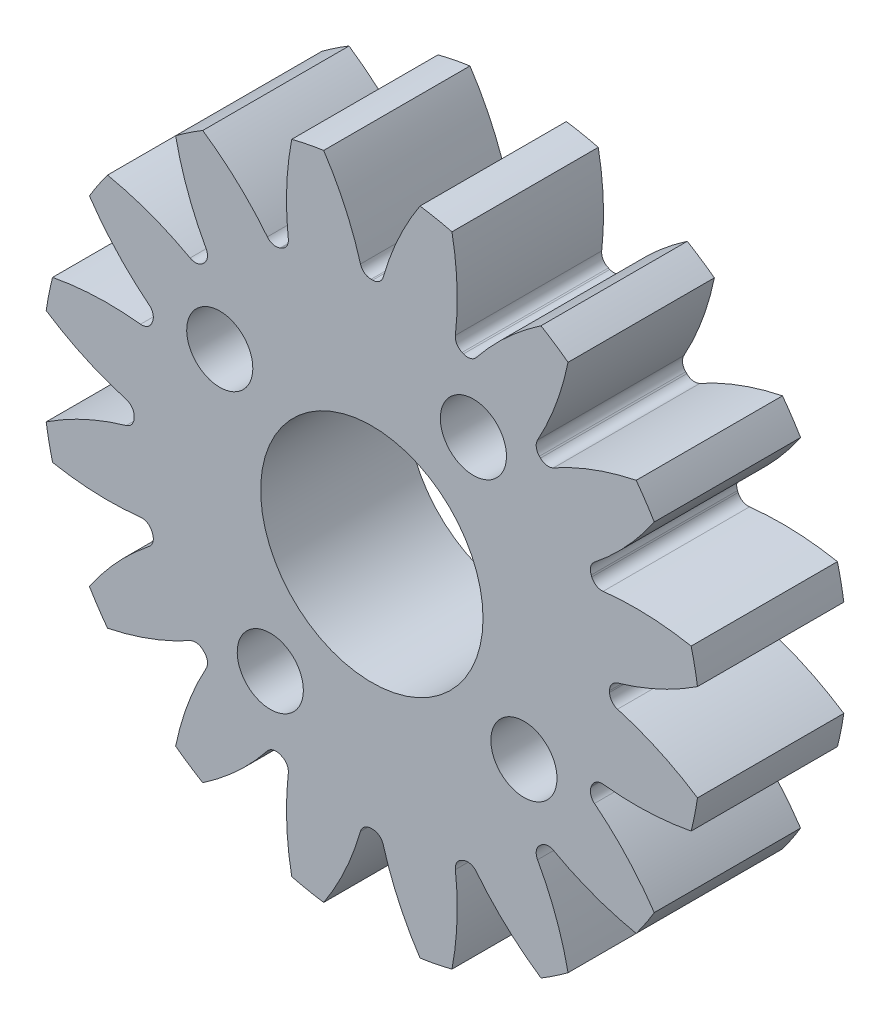
SolidWorks part; units mm, degrees
ref_plane "Front Plane" through (0, 0, 0) normal (0, 0, 1) x (1, 0, 0)
ref_plane "Top Plane" through (0, 0, 0) normal (0, 1, 0) x (1, 0, 0)
ref_plane "Right Plane" through (0, 0, 0) normal (1, 0, 0) x (0, 0, -1)
sketch "Sketch1" plane through (0, 0, 0) normal (0, 0, 1) x (1, 0, 0)
  line L0 (-203.2, 0) -> (203.2, 0) construction
  circle A0 centre (0, 0) radius 14.2875 construction
  circle A1 centre (0, 0) radius 12.7 construction
  circle A2 centre (0, 0) radius 10.3187 construction
  circle A3 centre (0, 0) radius 10.3251 construction
  circle A4 centre (0, 0) radius 6.35 construction
  circle A5 centre (0, 0) radius 10.3187 construction
  dimension "D2" = 1.5875
  dimension "D3" = 3.9688
  dimension "D1" = 3.9688
sketch "Sketch2" plane through (0, 0, 0) normal (1, 0, 0) x (0, 0, -1)
  line L0 (0, 0) -> (-19.05, 0) construction
  line L1 (-19.05, 0) -> (-31.75, 0) construction
  dimension "Overall Width" = 31.75
  dimension "Face Width" = 19.05
sketch "Sketch4" plane through (0, 0, 0) normal (1, 0, 0) x (0, 0, -1)
  line L0 (-31.75, 6.35) -> (-31.75, 10.3251)
  line L1 (-31.75, 10.3251) -> (-19.05, 10.3251)
  line L2 (-19.05, 10.3251) -> (-19.05, 14.2875)
  line L3 (-19.05, 14.2875) -> (0, 14.2875)
  line L4 (0, 14.2875) -> (0, 6.35)
  line L5 (-19.05, 10.3251) -> (-19.05, 0) construction
  line L6 (0, 14.2875) -> (0, -14.2875) construction
  line L7 (-19.05, 10.3251) -> (0, 10.3251) construction
  line L12 (-31.75, 6.35) -> (0, 6.35)
revolve "Revolve1" add sketch "Sketch4" angle 360 about L1
fillet "Fillet2" radius 0.2858 4 edges at (0, 10.3251, 31.75) (0, 10.3251, 19.05) (0, 14.2875, 19.05) (0, 14.2875, 0)
sketch "Sketch7" plane through (0, 0, 19.05) normal (0, 0, 1) x (1, 0, 0)
  line L0 (0, 0) -> (0, 14.2875) construction
  line L1 (1.2448, 12.6388) -> (1.9701, 14.151) construction
  line L3 (2.7874, 14.013) -> (2.4776, 12.456) construction
  line L4 (2.4776, 12.456) -> (2.0131, 10.1205) construction
  line L5 (0, 0) -> (2.0131, 10.1205) construction
  line L6 (1.2448, 12.6388) -> (0, 0) construction
  line L7 (1.2448, 12.6388) -> (1.4004, 14.2187) construction
  line L8 (1.2448, 12.6388) -> (0, 0) construction
  circle A0 centre (0, 0) radius 14.2875 construction
  arc A1 (-0.0331, 10.3187) -> (0.0331, 10.3187) centre (0, 0) cw
  circle A2 centre (0, 0) radius 10.3187 construction
  arc A3 (-1.2448, 12.6388) -> (1.2448, 12.6388) centre (0, 0) cw construction
  circle A4 centre (0, 0) radius 12.7 construction
  arc A5 (3.4772, 13.8579) -> (2.0907, 14.1337) centre (0, 0) ccw construction
  arc A6 (1.2448, 12.6388) -> (3.6866, 12.1531) centre (0, 0) cw construction
  arc A7 (-2.0907, 14.1337) -> (2.0907, 14.1337) centre (0, 0) cw
  arc A8 (0.4923, 10.6631) -> (2.0907, 14.1337) centre (12.6957, 7.1464) cw
  arc A9 (-0.4923, 10.6631) -> (-2.0907, 14.1337) centre (-12.6957, 7.1464) ccw
  arc A10 (-0.0331, 10.3187) -> (-0.4923, 10.6631) centre (-0.0346, 10.795) cw
  arc A11 (0.0331, 10.3187) -> (0.4923, 10.6631) centre (0.0346, 10.795) ccw
  point P26 (-0.3963, 10.3111)
  point P29 (0.3963, 10.3111)
  dimension "D4" = 0.4763
  dimension "D5" = 12.7
  dimension "D3" = 20
  dimension "D1" = 4.9873
  dimension "D2" = 2.4936
extrude "Cut-Extrude2" cut sketch "Sketch7" against normal through all
pattern_circular "CirPattern1" count 16 over 360 about axis through (0, 0, 0) along (0, 0, 1) of "Cut-Extrude2"
sketch "Sketch9" [suppressed] plane through (0, 0, 0) normal (0, 0, 1) x (1, 0, 0)
  circle A0 centre (0, 0) radius 10.3187 construction
  circle A1 centre (0, 0) radius 10.3187
ref_plane "Plane1" through (0, 0, 0) normal (0, 0, -1) x (-1, 0, 0)
ref_plane "Plane2" through (0, 0, 31.75) normal (0, 0, 1) x (1, 0, 0)
sketch "Sketch10" plane through (0, 0, 31.75) normal (0, 0, 1) x (1, 0, 0)
  circle A0 centre (0, 0) radius 29.0934
extrude "Cut-Extrude3" cut sketch "Sketch10" against normal blind 15.24
sketch "Sketch11" plane through (0, 0, 0) normal (0, 0, -1) x (-1, 0, 0)
  circle A0 centre (0, 0) radius 20.5552
extrude "Cut-Extrude4" cut sketch "Sketch11" against normal blind 10.16
sketch "Sketch12" plane through (0, 0, 16.51) normal (0, 0, 1) x (1, 0, 0)
  circle A0 centre (0, 0) radius 7.9171
  circle A1 centre (0, 0) radius 4.826
  dimension "D1" = 9.652
extrude "Boss-Extrude1" add sketch "Sketch12" against normal up to surface (6.35 mm away) up to face at (0, 6.35, 10.16)
sketch "Эскиз1" plane through (0, 0, 0) normal (0, 0, -1) x (-1, 0, 0)
  line L0 (0, 0) -> (17.9765, 12.0041) construction
  circle A0 centre (6.601, 4.408) radius 1.4351
  circle A1 centre (4.408, -6.601) radius 1.4351
  circle A2 centre (-6.601, -4.408) radius 1.4351
  circle A3 centre (-4.408, 6.601) radius 1.4351
  dimension "D3" = 2.8702
  dimension "D2" = 7.9375
  dimension "D1" = 4
extrude "Вырез-Вытянуть1" cut sketch "Эскиз1" against normal through all
sketch "Sketch13" plane through (0, 0, 16.51) normal (0, 0, 1) x (1, 0, 0)
  circle A0 centre (-4.408, -6.601) radius 1.4351 construction
  circle A1 centre (-4.408, -6.601) radius 1.4351
  circle A2 centre (6.601, -4.408) radius 1.4351 construction
  circle A3 centre (4.408, 6.601) radius 1.4351 construction
  circle A4 centre (-6.601, 4.408) radius 1.4351 construction
  circle A5 centre (6.601, -4.408) radius 1.4351
  circle A6 centre (4.408, 6.601) radius 1.4351
  circle A7 centre (-6.601, 4.408) radius 1.4351
  circle A8 centre (0, 0) radius 4.826 construction
  circle A9 centre (0, 0) radius 4.826
  arc A96 (-7.3402, -12.2578) -> (-4.5354, -9.663) centre (-14.4641, -1.7439) ccw
  arc A97 (-3.9794, -9.5206) -> (-4.5354, -9.663) centre (-4.1631, -9.96) ccw
  arc A98 (-3.9794, -9.5206) -> (-3.9182, -9.5459) centre (0, 0) ccw
  arc A99 (-3.6258, -10.0398) -> (-3.9182, -9.5459) centre (-4.099, -9.9865) ccw
  arc A100 (-3.6258, -10.0398) -> (-3.4772, -13.8579) centre (8.9945, -11.4608) ccw
  arc A101 (-3.4772, -13.8579) -> (-2.0907, -14.1337) centre (0, 0) ccw
  arc A102 (-2.0907, -14.1337) -> (-0.4923, -10.6631) centre (-12.6957, -7.1464) ccw
  arc A103 (-0.0331, -10.3187) -> (-0.4923, -10.6631) centre (-0.0346, -10.795) ccw
  arc A104 (-0.0331, -10.3187) -> (0.0331, -10.3187) centre (0, 0) ccw
  arc A105 (0.4923, -10.6631) -> (0.0331, -10.3187) centre (0.0346, -10.795) ccw
  arc A106 (0.4923, -10.6631) -> (2.0907, -14.1337) centre (12.6957, -7.1464) ccw
  arc A107 (2.0907, -14.1337) -> (3.4772, -13.8579) centre (0, 0) ccw
  arc A108 (3.4772, -13.8579) -> (3.6258, -10.0398) centre (-8.9945, -11.4608) ccw
  arc A109 (3.9182, -9.5459) -> (3.6258, -10.0398) centre (4.099, -9.9865) ccw
  arc A110 (3.9182, -9.5459) -> (3.9794, -9.5206) centre (0, 0) ccw
  arc A111 (4.5354, -9.663) -> (3.9794, -9.5206) centre (4.1631, -9.96) ccw
  arc A112 (4.5354, -9.663) -> (7.3402, -12.2578) centre (14.4641, -1.7439) ccw
  arc A113 (7.3402, -12.2578) -> (8.5157, -11.4724) centre (0, 0) ccw
  arc A114 (8.5157, -11.4724) -> (7.1918, -7.8881) centre (-3.924, -14.0305) ccw
  arc A115 (7.273, -7.3198) -> (7.1918, -7.8881) centre (7.6087, -7.6577) ccw
  arc A116 (7.273, -7.3198) -> (7.3198, -7.273) centre (0, 0) ccw
  arc A117 (7.8881, -7.1918) -> (7.3198, -7.273) centre (7.6577, -7.6087) ccw
  arc A118 (7.8881, -7.1918) -> (11.4724, -8.5157) centre (14.0305, 3.924) ccw
  arc A119 (11.4724, -8.5157) -> (12.2578, -7.3402) centre (0, 0) ccw
  arc A120 (12.2578, -7.3402) -> (9.663, -4.5354) centre (1.7439, -14.4641) ccw
  arc A121 (9.5206, -3.9794) -> (9.663, -4.5354) centre (9.96, -4.1631) ccw
  arc A122 (9.5206, -3.9794) -> (9.5459, -3.9182) centre (0, 0) ccw
  arc A123 (10.0398, -3.6258) -> (9.5459, -3.9182) centre (9.9865, -4.099) ccw
  arc A124 (10.0398, -3.6258) -> (13.8579, -3.4772) centre (11.4608, 8.9945) ccw
  arc A125 (13.8579, -3.4772) -> (14.1337, -2.0907) centre (0, 0) ccw
  arc A126 (14.1337, -2.0907) -> (10.6631, -0.4923) centre (7.1464, -12.6957) ccw
  arc A127 (10.3187, -0.0331) -> (10.6631, -0.4923) centre (10.795, -0.0346) ccw
  arc A128 (10.3187, -0.0331) -> (10.3187, 0.0331) centre (0, 0) ccw
  arc A129 (10.6631, 0.4923) -> (10.3187, 0.0331) centre (10.795, 0.0346) ccw
  arc A130 (10.6631, 0.4923) -> (14.1337, 2.0907) centre (7.1464, 12.6957) ccw
  arc A131 (14.1337, 2.0907) -> (13.8579, 3.4772) centre (0, 0) ccw
  arc A132 (13.8579, 3.4772) -> (10.0398, 3.6258) centre (11.4608, -8.9945) ccw
  arc A133 (9.5459, 3.9182) -> (10.0398, 3.6258) centre (9.9865, 4.099) ccw
  arc A134 (9.5459, 3.9182) -> (9.5206, 3.9794) centre (0, 0) ccw
  arc A135 (9.663, 4.5354) -> (9.5206, 3.9794) centre (9.96, 4.1631) ccw
  arc A136 (9.663, 4.5354) -> (12.2578, 7.3402) centre (1.7439, 14.4641) ccw
  arc A137 (12.2578, 7.3402) -> (11.4724, 8.5157) centre (0, 0) ccw
  arc A138 (11.4724, 8.5157) -> (7.8881, 7.1918) centre (14.0305, -3.924) ccw
  arc A139 (7.3198, 7.273) -> (7.8881, 7.1918) centre (7.6577, 7.6087) ccw
  arc A140 (7.3198, 7.273) -> (7.273, 7.3198) centre (0, 0) ccw
  arc A141 (7.1918, 7.8881) -> (7.273, 7.3198) centre (7.6087, 7.6577) ccw
  arc A142 (7.1918, 7.8881) -> (8.5157, 11.4724) centre (-3.924, 14.0305) ccw
  arc A143 (8.5157, 11.4724) -> (7.3402, 12.2578) centre (0, 0) ccw
  arc A144 (7.3402, 12.2578) -> (4.5354, 9.663) centre (14.4641, 1.7439) ccw
  arc A145 (3.9794, 9.5206) -> (4.5354, 9.663) centre (4.1631, 9.96) ccw
  arc A146 (3.9794, 9.5206) -> (3.9182, 9.5459) centre (0, 0) ccw
  arc A147 (3.6258, 10.0398) -> (3.9182, 9.5459) centre (4.099, 9.9865) ccw
  arc A148 (3.6258, 10.0398) -> (3.4772, 13.8579) centre (-8.9945, 11.4608) ccw
  arc A149 (3.4772, 13.8579) -> (2.0907, 14.1337) centre (0, 0) ccw
  arc A150 (2.0907, 14.1337) -> (0.4923, 10.6631) centre (12.6957, 7.1464) ccw
  arc A151 (0.0331, 10.3187) -> (0.4923, 10.6631) centre (0.0346, 10.795) ccw
  arc A152 (0.0331, 10.3187) -> (-0.0331, 10.3187) centre (0, 0) ccw
  arc A153 (-0.4923, 10.6631) -> (-0.0331, 10.3187) centre (-0.0346, 10.795) ccw
  arc A154 (-0.4923, 10.6631) -> (-2.0907, 14.1337) centre (-12.6957, 7.1464) ccw
  arc A155 (-2.0907, 14.1337) -> (-3.4772, 13.8579) centre (0, 0) ccw
  arc A156 (-3.4772, 13.8579) -> (-3.6258, 10.0398) centre (8.9945, 11.4608) ccw
  arc A157 (-3.9182, 9.5459) -> (-3.6258, 10.0398) centre (-4.099, 9.9865) ccw
  arc A158 (-3.9182, 9.5459) -> (-3.9794, 9.5206) centre (0, 0) ccw
  arc A159 (-4.5354, 9.663) -> (-3.9794, 9.5206) centre (-4.1631, 9.96) ccw
  arc A160 (-4.5354, 9.663) -> (-7.3402, 12.2578) centre (-14.4641, 1.7439) ccw
  arc A161 (-7.3402, 12.2578) -> (-8.5157, 11.4724) centre (0, 0) ccw
  arc A162 (-8.5157, 11.4724) -> (-7.1918, 7.8881) centre (3.924, 14.0305) ccw
  arc A163 (-7.273, 7.3198) -> (-7.1918, 7.8881) centre (-7.6087, 7.6577) ccw
  arc A164 (-7.273, 7.3198) -> (-7.3198, 7.273) centre (0, 0) ccw
  arc A165 (-7.8881, 7.1918) -> (-7.3198, 7.273) centre (-7.6577, 7.6087) ccw
  arc A166 (-7.8881, 7.1918) -> (-11.4724, 8.5157) centre (-14.0305, -3.924) ccw
  arc A167 (-11.4724, 8.5157) -> (-12.2578, 7.3402) centre (0, 0) ccw
  arc A168 (-12.2578, 7.3402) -> (-9.663, 4.5354) centre (-1.7439, 14.4641) ccw
  arc A169 (-9.5206, 3.9794) -> (-9.663, 4.5354) centre (-9.96, 4.1631) ccw
  arc A170 (-9.5206, 3.9794) -> (-9.5459, 3.9182) centre (0, 0) ccw
  arc A171 (-10.0398, 3.6258) -> (-9.5459, 3.9182) centre (-9.9865, 4.099) ccw
  arc A172 (-10.0398, 3.6258) -> (-13.8579, 3.4772) centre (-11.4608, -8.9945) ccw
  arc A173 (-13.8579, 3.4772) -> (-14.1337, 2.0907) centre (0, 0) ccw
  arc A174 (-14.1337, 2.0907) -> (-10.6631, 0.4923) centre (-7.1464, 12.6957) ccw
  arc A175 (-10.3187, 0.0331) -> (-10.6631, 0.4923) centre (-10.795, 0.0346) ccw
  arc A176 (-10.3187, 0.0331) -> (-10.3187, -0.0331) centre (0, 0) ccw
  arc A177 (-10.6631, -0.4923) -> (-10.3187, -0.0331) centre (-10.795, -0.0346) ccw
  arc A178 (-10.6631, -0.4923) -> (-14.1337, -2.0907) centre (-7.1464, -12.6957) ccw
  arc A179 (-14.1337, -2.0907) -> (-13.8579, -3.4772) centre (0, 0) ccw
  arc A180 (-13.8579, -3.4772) -> (-10.0398, -3.6258) centre (-11.4608, 8.9945) ccw
  arc A181 (-9.5459, -3.9182) -> (-10.0398, -3.6258) centre (-9.9865, -4.099) ccw
  arc A182 (-9.5459, -3.9182) -> (-9.5206, -3.9794) centre (0, 0) ccw
  arc A183 (-9.663, -4.5354) -> (-9.5206, -3.9794) centre (-9.96, -4.1631) ccw
  arc A184 (-9.663, -4.5354) -> (-12.2578, -7.3402) centre (-1.7439, -14.4641) ccw
  arc A185 (-12.2578, -7.3402) -> (-11.4724, -8.5157) centre (0, 0) ccw
  arc A186 (-11.4724, -8.5157) -> (-7.8881, -7.1918) centre (-14.0305, 3.924) ccw
  arc A187 (-7.3198, -7.273) -> (-7.8881, -7.1918) centre (-7.6577, -7.6087) ccw
  arc A188 (-7.3198, -7.273) -> (-7.273, -7.3198) centre (0, 0) ccw
  arc A189 (-7.1918, -7.8881) -> (-7.273, -7.3198) centre (-7.6087, -7.6577) ccw
  arc A190 (-7.1918, -7.8881) -> (-8.5157, -11.4724) centre (3.924, -14.0305) ccw
  arc A191 (-8.5157, -11.4724) -> (-7.3402, -12.2578) centre (0, 0) ccw
  arc A192 (-7.3402, -12.2578) -> (-4.5354, -9.663) centre (-14.4641, -1.7439) ccw
  arc A193 (-3.9794, -9.5206) -> (-4.5354, -9.663) centre (-4.1631, -9.96) ccw
  arc A194 (-3.9794, -9.5206) -> (-3.9182, -9.5459) centre (0, 0) ccw
  arc A195 (-3.6258, -10.0398) -> (-3.9182, -9.5459) centre (-4.099, -9.9865) ccw
  arc A196 (-3.6258, -10.0398) -> (-3.4772, -13.8579) centre (8.9945, -11.4608) ccw
  arc A197 (-3.4772, -13.8579) -> (-2.0907, -14.1337) centre (0, 0) ccw
  arc A198 (-2.0907, -14.1337) -> (-0.4923, -10.6631) centre (-12.6957, -7.1464) ccw
  arc A199 (-0.0331, -10.3187) -> (-0.4923, -10.6631) centre (-0.0346, -10.795) ccw
  arc A200 (-0.0331, -10.3187) -> (0.0331, -10.3187) centre (0, 0) ccw
  arc A201 (0.4923, -10.6631) -> (0.0331, -10.3187) centre (0.0346, -10.795) ccw
  arc A202 (0.4923, -10.6631) -> (2.0907, -14.1337) centre (12.6957, -7.1464) ccw
  arc A203 (2.0907, -14.1337) -> (3.4772, -13.8579) centre (0, 0) ccw
  arc A204 (3.4772, -13.8579) -> (3.6258, -10.0398) centre (-8.9945, -11.4608) ccw
  arc A205 (3.9182, -9.5459) -> (3.6258, -10.0398) centre (4.099, -9.9865) ccw
  arc A206 (3.9182, -9.5459) -> (3.9794, -9.5206) centre (0, 0) ccw
  arc A207 (4.5354, -9.663) -> (3.9794, -9.5206) centre (4.1631, -9.96) ccw
  arc A208 (4.5354, -9.663) -> (7.3402, -12.2578) centre (14.4641, -1.7439) ccw
  arc A209 (7.3402, -12.2578) -> (8.5157, -11.4724) centre (0, 0) ccw
  arc A210 (8.5157, -11.4724) -> (7.1918, -7.8881) centre (-3.924, -14.0305) ccw
  arc A211 (7.273, -7.3198) -> (7.1918, -7.8881) centre (7.6087, -7.6577) ccw
  arc A212 (7.273, -7.3198) -> (7.3198, -7.273) centre (0, 0) ccw
  arc A213 (7.8881, -7.1918) -> (7.3198, -7.273) centre (7.6577, -7.6087) ccw
  arc A214 (7.8881, -7.1918) -> (11.4724, -8.5157) centre (14.0305, 3.924) ccw
  arc A215 (11.4724, -8.5157) -> (12.2578, -7.3402) centre (0, 0) ccw
  arc A216 (12.2578, -7.3402) -> (9.663, -4.5354) centre (1.7439, -14.4641) ccw
  arc A217 (9.5206, -3.9794) -> (9.663, -4.5354) centre (9.96, -4.1631) ccw
  arc A218 (9.5206, -3.9794) -> (9.5459, -3.9182) centre (0, 0) ccw
  arc A219 (10.0398, -3.6258) -> (9.5459, -3.9182) centre (9.9865, -4.099) ccw
  arc A220 (10.0398, -3.6258) -> (13.8579, -3.4772) centre (11.4608, 8.9945) ccw
  arc A221 (13.8579, -3.4772) -> (14.1337, -2.0907) centre (0, 0) ccw
  arc A222 (14.1337, -2.0907) -> (10.6631, -0.4923) centre (7.1464, -12.6957) ccw
  arc A223 (10.3187, -0.0331) -> (10.6631, -0.4923) centre (10.795, -0.0346) ccw
  arc A224 (10.3187, -0.0331) -> (10.3187, 0.0331) centre (0, 0) ccw
  arc A225 (10.6631, 0.4923) -> (10.3187, 0.0331) centre (10.795, 0.0346) ccw
  arc A226 (10.6631, 0.4923) -> (14.1337, 2.0907) centre (7.1464, 12.6957) ccw
  arc A227 (14.1337, 2.0907) -> (13.8579, 3.4772) centre (0, 0) ccw
  arc A228 (13.8579, 3.4772) -> (10.0398, 3.6258) centre (11.4608, -8.9945) ccw
  arc A229 (9.5459, 3.9182) -> (10.0398, 3.6258) centre (9.9865, 4.099) ccw
  arc A230 (9.5459, 3.9182) -> (9.5206, 3.9794) centre (0, 0) ccw
  arc A231 (9.663, 4.5354) -> (9.5206, 3.9794) centre (9.96, 4.1631) ccw
  arc A232 (9.663, 4.5354) -> (12.2578, 7.3402) centre (1.7439, 14.4641) ccw
  arc A233 (12.2578, 7.3402) -> (11.4724, 8.5157) centre (0, 0) ccw
  arc A234 (11.4724, 8.5157) -> (7.8881, 7.1918) centre (14.0305, -3.924) ccw
  arc A235 (7.3198, 7.273) -> (7.8881, 7.1918) centre (7.6577, 7.6087) ccw
  arc A236 (7.3198, 7.273) -> (7.273, 7.3198) centre (0, 0) ccw
  arc A237 (7.1918, 7.8881) -> (7.273, 7.3198) centre (7.6087, 7.6577) ccw
  arc A238 (7.1918, 7.8881) -> (8.5157, 11.4724) centre (-3.924, 14.0305) ccw
  arc A239 (8.5157, 11.4724) -> (7.3402, 12.2578) centre (0, 0) ccw
  arc A240 (7.3402, 12.2578) -> (4.5354, 9.663) centre (14.4641, 1.7439) ccw
  arc A241 (3.9794, 9.5206) -> (4.5354, 9.663) centre (4.1631, 9.96) ccw
  arc A242 (3.9794, 9.5206) -> (3.9182, 9.5459) centre (0, 0) ccw
  arc A243 (3.6258, 10.0398) -> (3.9182, 9.5459) centre (4.099, 9.9865) ccw
  arc A244 (3.6258, 10.0398) -> (3.4772, 13.8579) centre (-8.9945, 11.4608) ccw
  arc A245 (3.4772, 13.8579) -> (2.0907, 14.1337) centre (0, 0) ccw
  arc A246 (2.0907, 14.1337) -> (0.4923, 10.6631) centre (12.6957, 7.1464) ccw
  arc A247 (0.0331, 10.3187) -> (0.4923, 10.6631) centre (0.0346, 10.795) ccw
  arc A248 (0.0331, 10.3187) -> (-0.0331, 10.3187) centre (0, 0) ccw
  arc A249 (-0.4923, 10.6631) -> (-0.0331, 10.3187) centre (-0.0346, 10.795) ccw
  arc A250 (-0.4923, 10.6631) -> (-2.0907, 14.1337) centre (-12.6957, 7.1464) ccw
  arc A251 (-2.0907, 14.1337) -> (-3.4772, 13.8579) centre (0, 0) ccw
  arc A252 (-3.4772, 13.8579) -> (-3.6258, 10.0398) centre (8.9945, 11.4608) ccw
  arc A253 (-3.9182, 9.5459) -> (-3.6258, 10.0398) centre (-4.099, 9.9865) ccw
  arc A254 (-3.9182, 9.5459) -> (-3.9794, 9.5206) centre (0, 0) ccw
  arc A255 (-4.5354, 9.663) -> (-3.9794, 9.5206) centre (-4.1631, 9.96) ccw
  arc A256 (-4.5354, 9.663) -> (-7.3402, 12.2578) centre (-14.4641, 1.7439) ccw
  arc A257 (-7.3402, 12.2578) -> (-8.5157, 11.4724) centre (0, 0) ccw
  arc A258 (-8.5157, 11.4724) -> (-7.1918, 7.8881) centre (3.924, 14.0305) ccw
  arc A259 (-7.273, 7.3198) -> (-7.1918, 7.8881) centre (-7.6087, 7.6577) ccw
  arc A260 (-7.273, 7.3198) -> (-7.3198, 7.273) centre (0, 0) ccw
  arc A261 (-7.8881, 7.1918) -> (-7.3198, 7.273) centre (-7.6577, 7.6087) ccw
  arc A262 (-7.8881, 7.1918) -> (-11.4724, 8.5157) centre (-14.0305, -3.924) ccw
  arc A263 (-11.4724, 8.5157) -> (-12.2578, 7.3402) centre (0, 0) ccw
  arc A264 (-12.2578, 7.3402) -> (-9.663, 4.5354) centre (-1.7439, 14.4641) ccw
  arc A265 (-9.5206, 3.9794) -> (-9.663, 4.5354) centre (-9.96, 4.1631) ccw
  arc A266 (-9.5206, 3.9794) -> (-9.5459, 3.9182) centre (0, 0) ccw
  arc A267 (-10.0398, 3.6258) -> (-9.5459, 3.9182) centre (-9.9865, 4.099) ccw
  arc A268 (-10.0398, 3.6258) -> (-13.8579, 3.4772) centre (-11.4608, -8.9945) ccw
  arc A269 (-13.8579, 3.4772) -> (-14.1337, 2.0907) centre (0, 0) ccw
  arc A270 (-14.1337, 2.0907) -> (-10.6631, 0.4923) centre (-7.1464, 12.6957) ccw
  arc A271 (-10.3187, 0.0331) -> (-10.6631, 0.4923) centre (-10.795, 0.0346) ccw
  arc A272 (-10.3187, 0.0331) -> (-10.3187, -0.0331) centre (0, 0) ccw
  arc A273 (-10.6631, -0.4923) -> (-10.3187, -0.0331) centre (-10.795, -0.0346) ccw
  arc A274 (-10.6631, -0.4923) -> (-14.1337, -2.0907) centre (-7.1464, -12.6957) ccw
  arc A275 (-14.1337, -2.0907) -> (-13.8579, -3.4772) centre (0, 0) ccw
  arc A276 (-13.8579, -3.4772) -> (-10.0398, -3.6258) centre (-11.4608, 8.9945) ccw
  arc A277 (-9.5459, -3.9182) -> (-10.0398, -3.6258) centre (-9.9865, -4.099) ccw
  arc A278 (-9.5459, -3.9182) -> (-9.5206, -3.9794) centre (0, 0) ccw
  arc A279 (-9.663, -4.5354) -> (-9.5206, -3.9794) centre (-9.96, -4.1631) ccw
  arc A280 (-9.663, -4.5354) -> (-12.2578, -7.3402) centre (-1.7439, -14.4641) ccw
  arc A281 (-12.2578, -7.3402) -> (-11.4724, -8.5157) centre (0, 0) ccw
  arc A282 (-11.4724, -8.5157) -> (-7.8881, -7.1918) centre (-14.0305, 3.924) ccw
  arc A283 (-7.3198, -7.273) -> (-7.8881, -7.1918) centre (-7.6577, -7.6087) ccw
  arc A284 (-7.3198, -7.273) -> (-7.273, -7.3198) centre (0, 0) ccw
  arc A285 (-7.1918, -7.8881) -> (-7.273, -7.3198) centre (-7.6087, -7.6577) ccw
  arc A286 (-7.1918, -7.8881) -> (-8.5157, -11.4724) centre (3.924, -14.0305) ccw
  arc A287 (-8.5157, -11.4724) -> (-7.3402, -12.2578) centre (0, 0) ccw
  dimension "D1" = 0
equation "\"D1@Sketch1\"=2.5*(\"Pitch Dia.@Sketch1\"/\"Number of Teeth@Sketch1\")"
equation "\"D1@CirPattern1\"=\"Number of Teeth@Sketch1\""
equation "\"D1@Fillet2\"=\"OD@Sketch1\"*.01"
equation "\"D1@Sketch7\"=3.14159*(\"Pitch Dia.@Sketch1\"/\"Number of Teeth@Sketch1\")"
equation "\"D2@Sketch7\"=\"D1@Sketch7\"/2"
equation "\"D4@Sketch7\"=\"D1@Sketch7\"*.0955"
equation "\"D5@Sketch7\"=\"Pitch Dia.@Sketch1\"/2"
